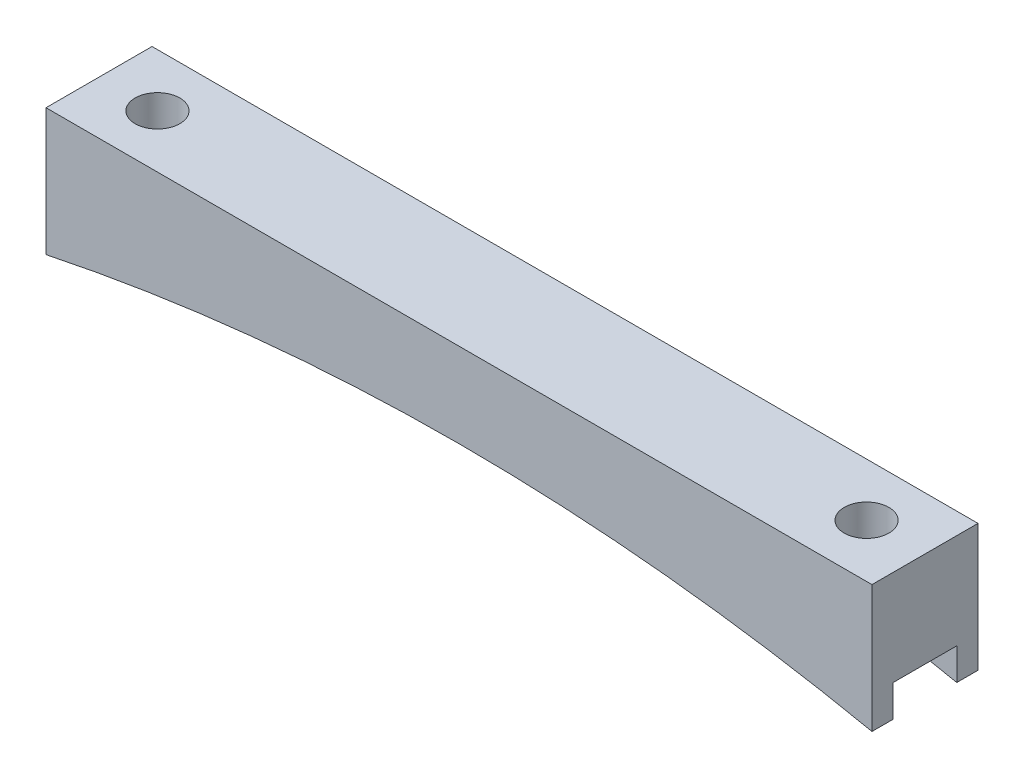
SolidWorks part; units mm, degrees
ref_plane "Front Plane" through (0, 0, 0) normal (0, 0, 1) x (1, 0, 0)
ref_plane "Top Plane" through (0, 0, 0) normal (0, 1, 0) x (1, 0, 0)
ref_plane "Right Plane" through (0, 0, 0) normal (1, 0, 0) x (0, 0, -1)
sketch "Sketch1" plane through (0, 0, 0) normal (0, 0, 1) x (1, 0, 0)
  line L0 (-49.465, 0) -> (49.465, 0)
  line L1 (-42.465, -2.54) -> (42.465, -2.54) construction
  line L2 (0, 0) -> (0, -4.6068) construction
  line L3 (49.465, 0) -> (49.465, -15.24)
  line L4 (-49.465, 0) -> (-49.465, -15.24)
  arc A0 (-49.465, -15.24) -> (49.465, -15.24) centre (0, -251.4156) cw
  point P4 (0, 0)
  point P9 (0, -2.54)
  dimension "D4" = 241.3
  dimension "D1" = 84.93
  dimension "D2" = 2.54
  dimension "D3" = 7
  dimension "D5" = 15.24
extrude "Boss-Extrude1" add sketch "Sketch1" along normal blind 12.7
sketch "Sketch2" plane through (0, 0, 0) normal (0, 1, 0) x (1, 0, 0)
  line L1 (-42.465, 0) -> (-42.465, -12.7) construction
  line L2 (-49.465, 0) -> (49.465, 0) construction
  line L3 (49.465, -12.7) -> (-49.465, -12.7) construction
  line L4 (42.465, 0) -> (42.465, -12.7) construction
  circle A0 centre (-42.465, -6.35) radius 2.675
  circle A1 centre (42.465, -6.35) radius 2.675
  circle A2 centre (-42.465, -6.35) radius 3 construction
  point P7 (-42.465, -6.35)
  dimension "D1" = 5.35
  dimension "D2" = 6
extrude "Cut-Extrude1" cut sketch "Sketch2" against normal through all
sketch "Sketch3" plane through (49.465, 0, 0) normal (1, 0, 0) x (0, 0, -1)
  line L0 (-12.7, -15.24) -> (0, -15.24) construction
  line L1 (-10.16, -15.24) -> (-2.54, -15.24)
  line L2 (-10.16, -15.24) -> (-10.16, -11.43)
  line L3 (-10.16, -11.43) -> (-2.54, -11.43)
  line L4 (-2.54, -15.24) -> (-2.54, -11.43)
  line L5 (-12.7, -15.24) -> (-12.7, 0) construction
  line L6 (0, -15.24) -> (0, 0) construction
  dimension "D1" = 2.54
  dimension "D2" = 2.54
  dimension "D3" = 3.81
extrude "Cut-Extrude2" cut sketch "Sketch3" against normal through all
